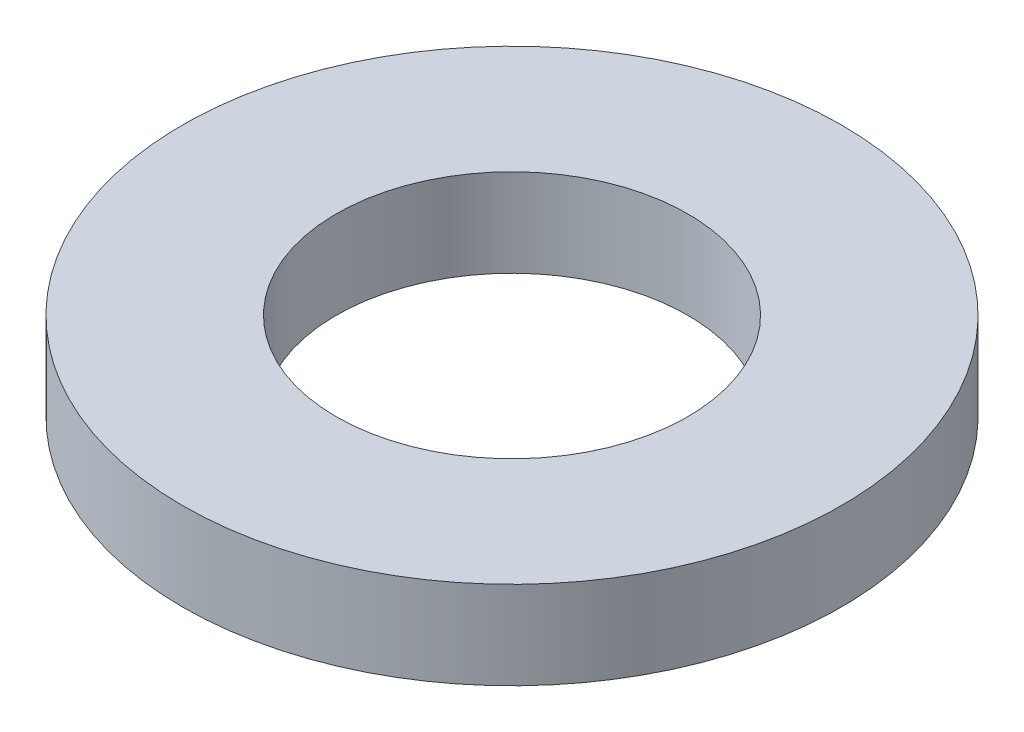
SolidWorks part; units mm, degrees
ref_plane "Alzado" through (0, 0, 0) normal (0, 0, 1) x (1, 0, 0)
ref_plane "Planta" through (0, 0, 0) normal (0, 1, 0) x (1, 0, 0)
ref_plane "Vista lateral" through (0, 0, 0) normal (1, 0, 0) x (0, 0, -1)
sketch "Croquis1" plane through (0, 0, 0) normal (0, 1, 0) x (1, 0, 0)
  circle A0 centre (0, 0) radius 7.5
  dimension "D1" = 15
extrude "Saliente-Extruir1" add sketch "Croquis1" along normal blind 2
sketch "Croquis2" plane through (0, 0, 0) normal (0, 1, 0) x (1, 0, 0)
  circle A0 centre (0, 0) radius 4
  dimension "D1" = 8
extrude "Cortar-Extruir1" cut sketch "Croquis2" along normal through all
